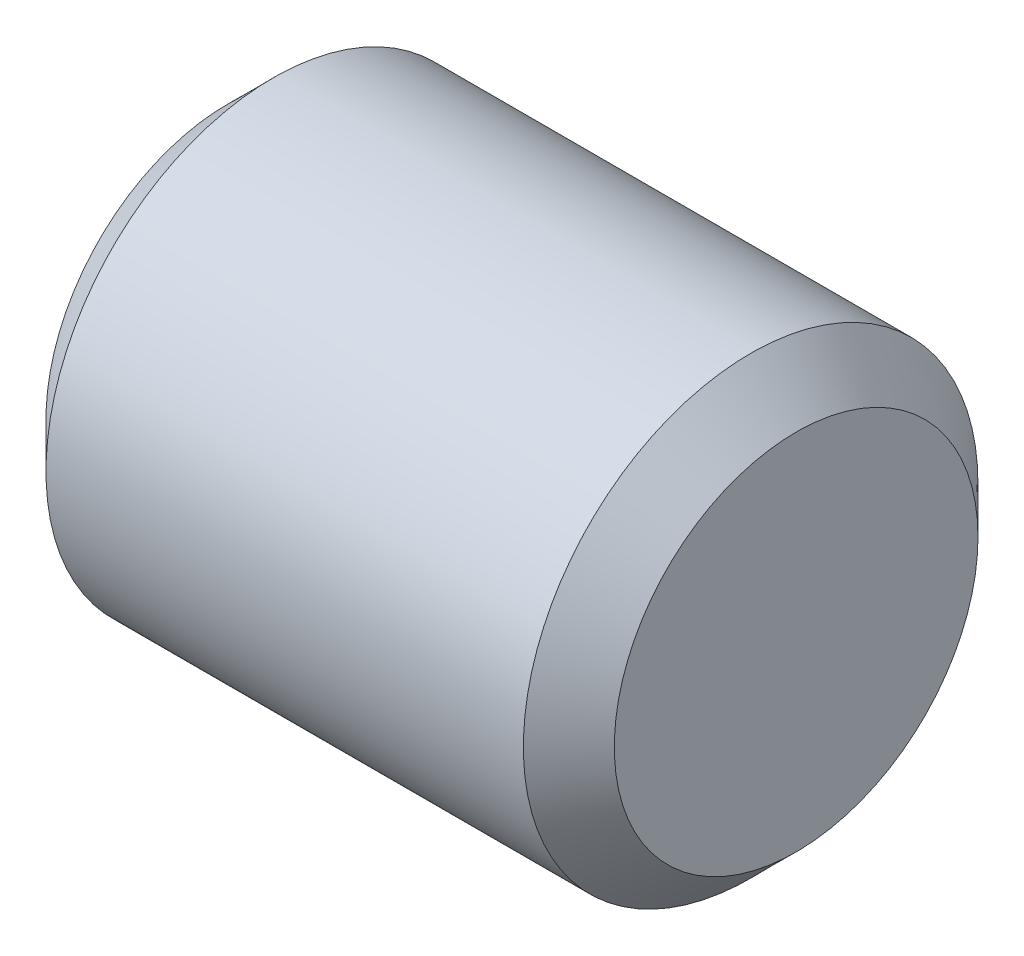
SolidWorks part; units mm, degrees
ref_plane "Front" through (0, 0, 0) normal (0, 0, 1) x (1, 0, 0)
ref_plane "Top" through (0, 0, 0) normal (0, 1, 0) x (1, 0, 0)
ref_plane "Right" through (0, 0, 0) normal (1, 0, 0) x (0, 0, -1)
sketch "Sketch1" plane through (0, 0, 0) normal (0, 0, 1) x (1, 0, 0)
  line L0 (-3.9688, 0) -> (3.9688, 0) construction
  line L1 (3.9688, 3.175) -> (3.9688, -3.175) construction
  line L2 (-3.9688, 3.175) -> (-3.9688, -3.175) construction
  dimension "Length" = 7.9375
  dimension "Diameter" = 6.35
sketch "Sketch2" plane through (0, 0, 0) normal (1, 0, 0) x (0, 0, -1)
  circle A0 centre (0, 0) radius 3.175
extrude "Extrude1" add sketch "Sketch2" against normal up to vertex (3.9688 mm away) and the other way up to vertex (3.9688 mm away) up to point (-3.9688, 3.175, 0) other way up to point (3.9688, 3.175, 0)
chamfer "Chamfer1" distance 0.635 angle 45 2 edges at (3.9688, 0, -3.175) (-3.9688, 0, -3.175)
equation "\"D1@Chamfer1\" = \"Diameter@Sketch1\"*.1"
